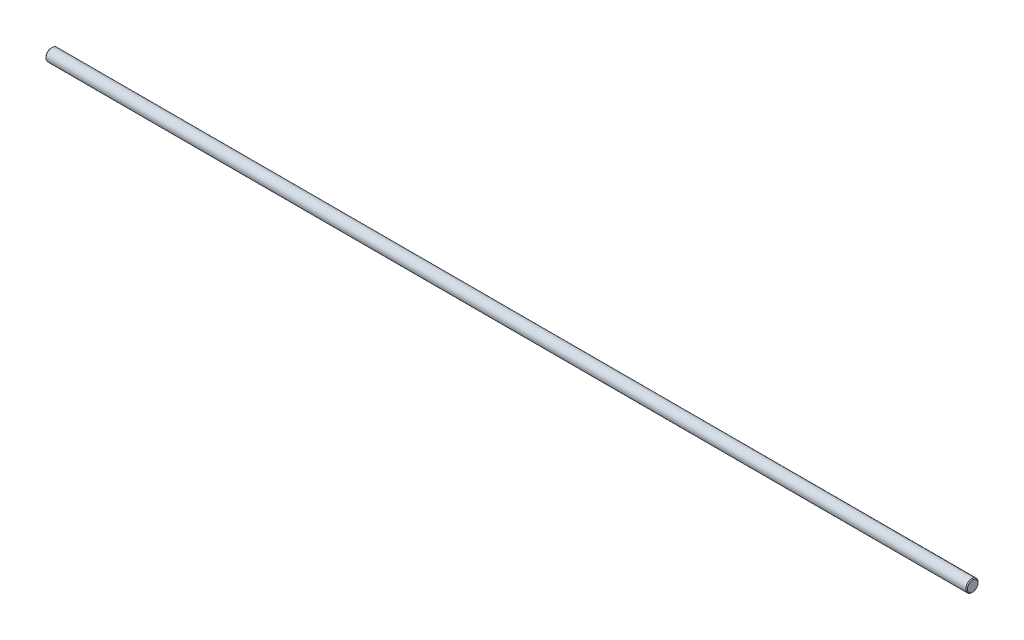
SolidWorks part; units mm, degrees
ref_plane "Plan de face" through (0, 0, 0) normal (0, 0, 1) x (1, 0, 0)
ref_plane "Plan de dessus" through (0, 0, 0) normal (0, 1, 0) x (1, 0, 0)
ref_plane "Plan de droite" through (0, 0, 0) normal (1, 0, 0) x (0, 0, -1)
sketch "Esquisse1" plane through (0, 0, 0) normal (1, 0, 0) x (0, 0, -1)
  circle A0 centre (0, 0) radius 1.5
extrude "Boss.-Extru.1" add sketch "Esquisse1" along normal blind 226
chamfer "Chanfrein1" distance 0.2 angle 45 2 edges at (0, 0, -1.5) (226, 0, -1.5)
